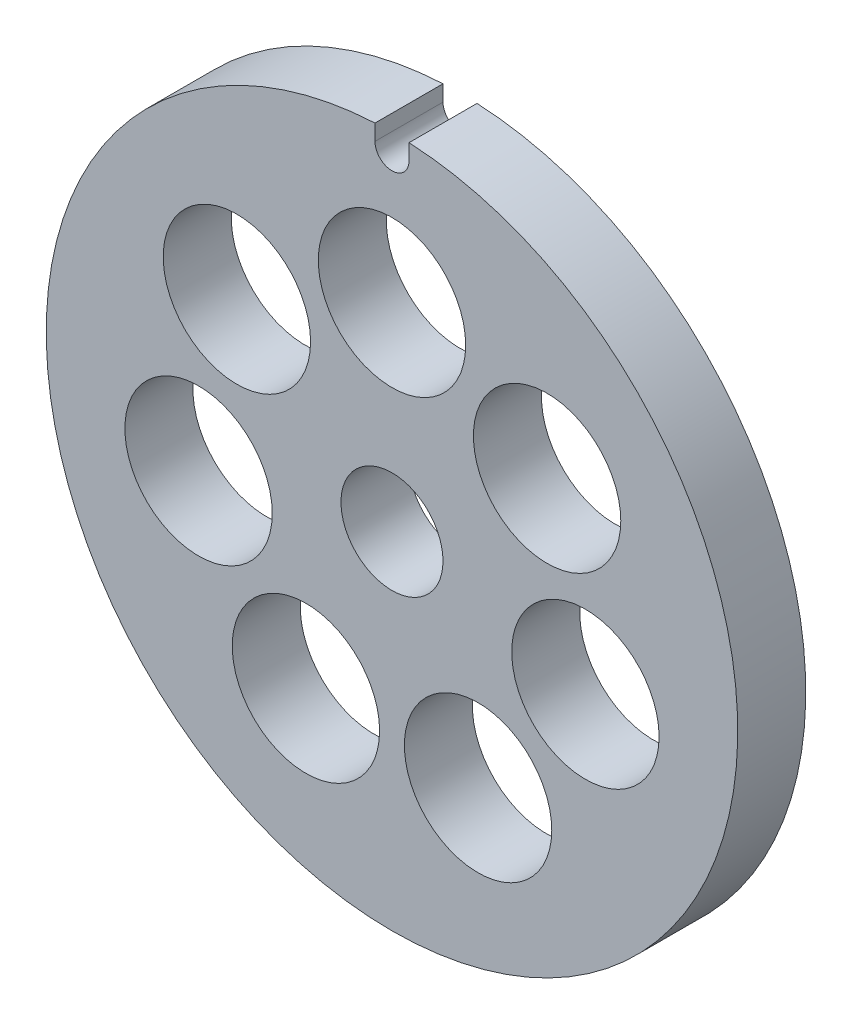
SolidWorks part; units mm, degrees
ref_plane "Płaszczyzna przednia" through (0, 0, 0) normal (0, 0, 1) x (1, 0, 0)
ref_plane "Płaszczyzna górna" through (0, 0, 0) normal (0, 1, 0) x (1, 0, 0)
ref_plane "Płaszczyzna prawa" through (0, 0, 0) normal (1, 0, 0) x (0, 0, -1)
sketch "Szkic1" plane through (0, 0, 0) normal (0, 0, 1) x (1, 0, 0)
  line L0 (-1.5, 30.4631) -> (-1.5, 29.0631)
  line L1 (1.5, 29.0631) -> (1.5, 30.4631)
  circle A0 centre (0, 0) radius 4.5
  arc A1 (-1.5, 30.4631) -> (1.5, 30.4631) centre (0, 0) ccw
  circle A2 centre (0, 17.5) radius 6.5
  circle A3 centre (13.6821, 10.9111) radius 6.5
  circle A4 centre (17.0612, -3.8941) radius 6.5
  circle A5 centre (7.593, -15.767) radius 6.5
  circle A6 centre (-7.593, -15.767) radius 6.5
  circle A7 centre (-17.0612, -3.8941) radius 6.5
  circle A8 centre (-13.6821, 10.9111) radius 6.5
  arc A9 (-1.5, 29.0631) -> (1.5, 29.0631) centre (0, 29.0631) ccw
  point P20 (0, 0)
  point P23 (0, 0)
  dimension "D1" = 9
  dimension "D2" = 61
  dimension "D3" = 13
  dimension "D4" = 17.5
  dimension "D6" = 1.4
  dimension "D7" = 1.5
  dimension "D5" = 7
extrude "Dodanie-wyciągnięcie2" add sketch "Szkic1" along normal blind 6
